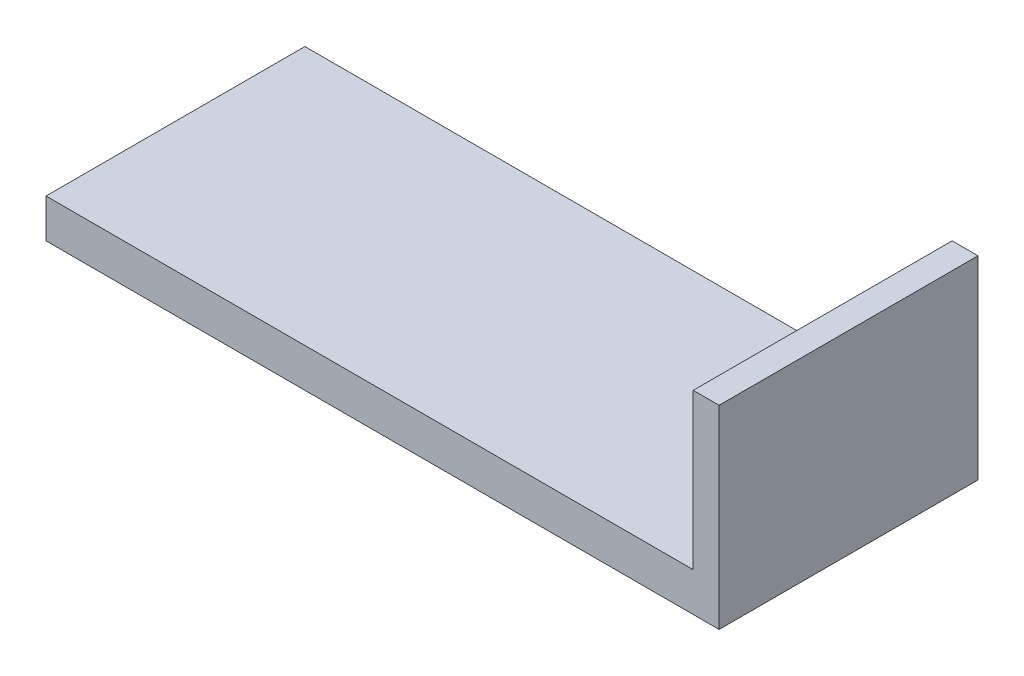
SolidWorks part; units mm, degrees
ref_plane "Front Plane" through (0, 0, 0) normal (0, 0, 1) x (1, 0, 0)
ref_plane "Top Plane" through (0, 0, 0) normal (0, 1, 0) x (1, 0, 0)
ref_plane "Right Plane" through (0, 0, 0) normal (1, 0, 0) x (0, 0, -1)
sketch "Sketch1" plane through (0, 0, 0) normal (0, 0, 1) x (1, 0, 0)
  line L0 (0, 0) -> (5000, 0)
  line L1 (5000, 0) -> (5000, 1200)
  line L2 (5000, 1200) -> (5200, 1200)
  line L3 (5200, 1200) -> (5200, -300)
  line L4 (5200, -300) -> (0, -300)
  line L5 (0, -300) -> (0, 0)
  dimension "D1" = 5000
  dimension "D2" = 300
  dimension "D3" = 1200
  dimension "D4" = 200
extrude "Boss-Extrude1" add sketch "Sketch1" along normal blind 2000
